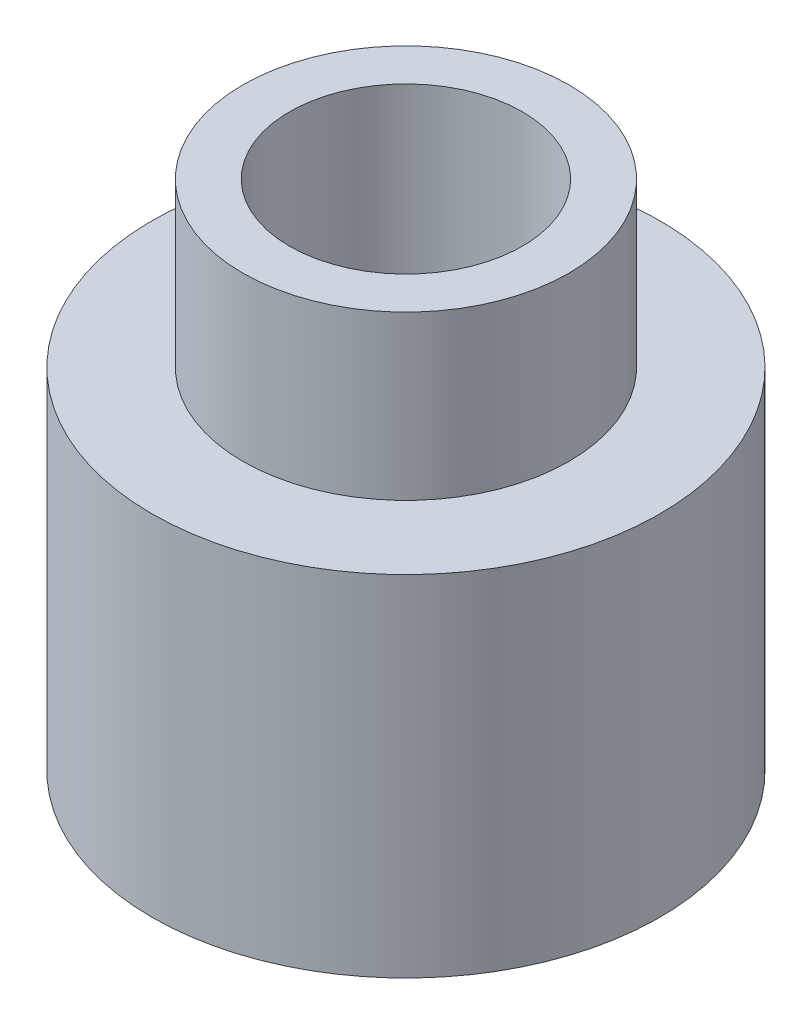
SolidWorks part; units mm, degrees
ref_plane "Спереди" through (0, 0, 0) normal (0, 0, 1) x (1, 0, 0)
ref_plane "Сверху" through (0, 0, 0) normal (0, 1, 0) x (1, 0, 0)
ref_plane "Справа" through (0, 0, 0) normal (1, 0, 0) x (0, 0, -1)
sketch "Эскиз1" plane through (0, 0, 0) normal (0, 1, 0) x (1, 0, 0)
  circle A0 centre (0, 0) radius 2.18
extrude "Бобышка-Вытянуть1" add sketch "Эскиз1" along normal blind 3
sketch "Эскиз2" plane through (0, 3, 0) normal (0, 1, 0) x (1, 0, 0)
  circle A0 centre (0, 0) radius 1.4
extrude "Бобышка-Вытянуть2" add sketch "Эскиз2" along normal blind 1.4
sketch "Эскиз3" plane through (0, 4.4, 0) normal (0, 1, 0) x (1, 0, 0)
  circle A0 centre (0, 0) radius 1
extrude "Вырез-Вытянуть1" cut sketch "Эскиз3" against normal blind 10
